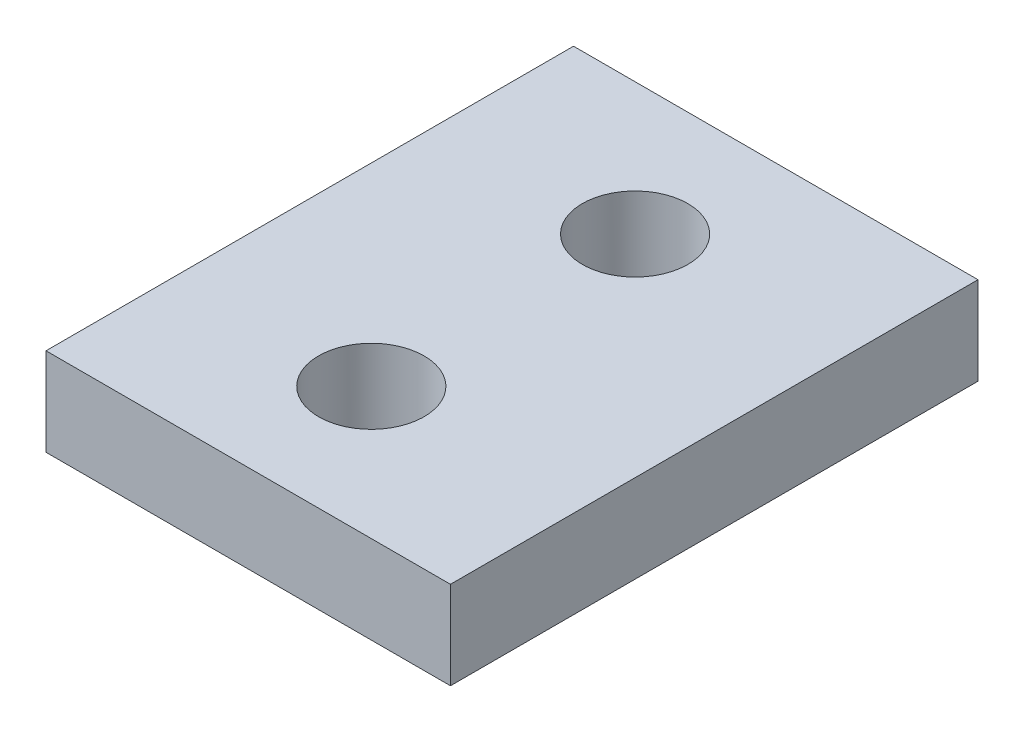
SolidWorks part; units mm, degrees
ref_plane "Ebene vorne" through (0, 0, 0) normal (0, 0, 1) x (1, 0, 0)
ref_plane "Ebene oben" through (0, 0, 0) normal (0, 1, 0) x (1, 0, 0)
ref_plane "Ebene rechts" through (0, 0, 0) normal (1, 0, 0) x (0, 0, -1)
sketch "Skizze1" plane through (0, 0, 0) normal (0, 1, 0) x (1, 0, 0)
  line L1 (0, 0) -> (30.9843, 0) construction
  line L4 (-65, -15) -> (65, -15)
  line L5 (-65, -15) -> (-65, 15)
  line L6 (-65, 15) -> (65, 15)
  line L7 (65, -15) -> (65, 15)
  line L8 (-65, -15) -> (65, 15) construction
  line L9 (-65, 15) -> (65, -15) construction
  circle A0 centre (53, -7.5) radius 1.65
  circle A1 centre (53, 7.5) radius 1.65
  circle A2 centre (-53, 7.5) radius 1.65
  circle A3 centre (-53, -7.5) radius 1.65
  point P8 (0, 0)
sketch "Skizze2" plane through (0, 0, 0) normal (0, 0, 1) x (1, 0, 0)
  line L1 (65, 16) -> (42, 16)
  line L2 (65, 16) -> (65, 11)
  line L3 (65, 11) -> (42, 11)
  line L4 (42, 16) -> (42, 11)
sketch "Skizze4" plane through (0, 0, 0) normal (0, 0, 1) x (1, 0, 0)
  line L1 (42, 16) -> (65, 16)
  line L2 (42, 16) -> (42, 11)
  line L3 (42, 11) -> (65, 11)
  line L4 (65, 16) -> (65, 11)
sketch "Skizze5" plane through (0, 0, 0) normal (1, 0, 0) x (0, 0, -1)
  line L0 (15, 0) -> (-15, 0)
  point P8 (0, 0)
sketch "Skizze6" plane through (0, 0, 0) normal (0, 1, 0) x (1, 0, 0)
  circle A0 centre (53, 7.5) radius 3
  circle A1 centre (53, -7.5) radius 3
  dimension "D1" = 6
  dimension "D2" = 6
extrude "Aufsatz-Linear austragen1" add sketch "Skizze4" along normal up to vertex (15 mm away) and the other way up to vertex (15 mm away) up to point (0, 0, 15) other way up to point (0, 0, -15)
extrude "Schnitt-Linear austragen1" cut sketch "Skizze6" along normal up to surface (16 mm away) up to face at (53.5, 16, 0)
